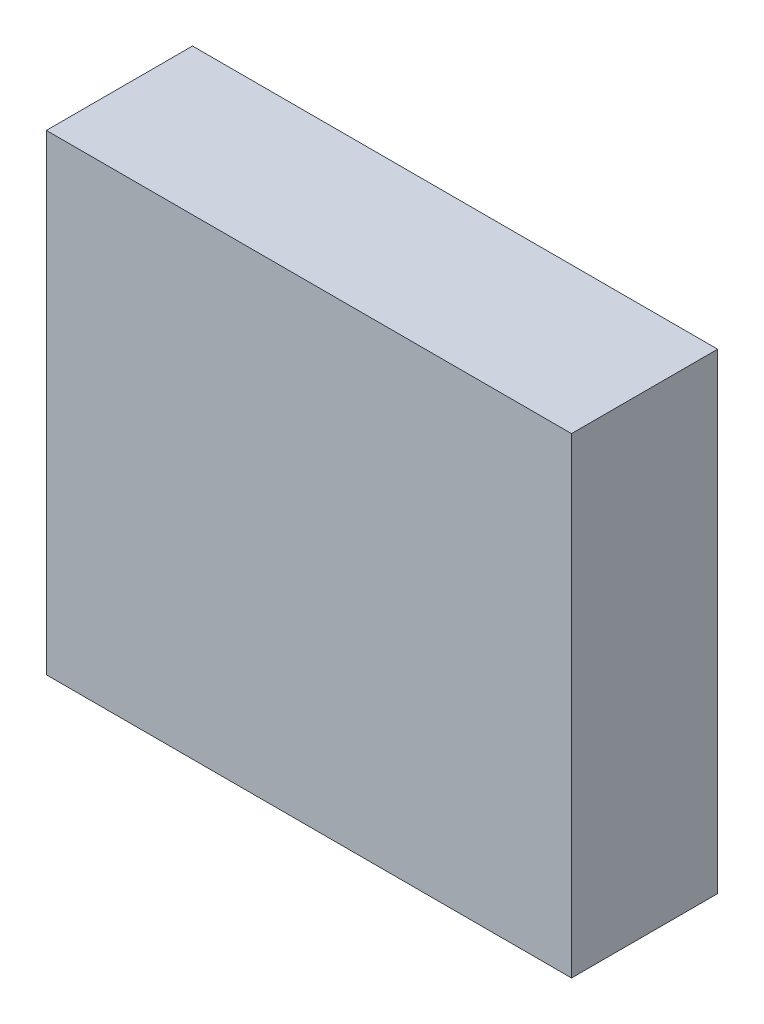
SolidWorks part; units mm, degrees
ref_plane "Front Plane" through (0, 0, 0) normal (0, 0, 1) x (1, 0, 0)
ref_plane "Top Plane" through (0, 0, 0) normal (0, 1, 0) x (1, 0, 0)
ref_plane "Right Plane" through (0, 0, 0) normal (1, 0, 0) x (0, 0, -1)
sketch "Sketch1" plane through (0, 0, 0) normal (0, 1, 0) x (1, 0, 0)
  line L1 (0, 0) -> (323.088, 0)
  line L2 (0, 0) -> (0, 89.916)
  line L3 (0, 89.916) -> (323.088, 89.916)
  line L4 (323.088, 0) -> (323.088, 89.916)
  dimension "D1" = 89.916
  dimension "D2" = 323.088
extrude "Boss-Extrude1" add sketch "Sketch1" along normal blind 290.068
sketch "Sketch2" plane through (0, 290.068, 0) normal (0, 1, 0) x (1, 0, 0)
  line L0 (0, 89.916) -> (0, 0) construction
  line L1 (0, 0) -> (323.088, 0) construction
  line L2 (323.088, 0) -> (323.088, 89.916) construction
  line L3 (5.08, 84.836) -> (318.008, 84.836)
  line L4 (5.08, 84.836) -> (5.08, 5.08)
  line L5 (5.08, 5.08) -> (318.008, 5.08)
  line L6 (318.008, 84.836) -> (318.008, 5.08)
  line L7 (5.08, 84.836) -> (318.008, 5.08) construction
  line L8 (5.08, 5.08) -> (318.008, 84.836) construction
  line L9 (161.544, 0) -> (161.544, 84.1525) construction
  line L10 (0, 44.958) -> (183.1052, 44.958) construction
  point P0 (0, 44.958)
  point P1 (161.544, 0)
  point P4 (161.544, 44.958)
  dimension "D1" = 5.08
  dimension "D2" = 5.08
extrude "Cut-Extrude1" cut sketch "Sketch2" against normal through all from offset 5.08
